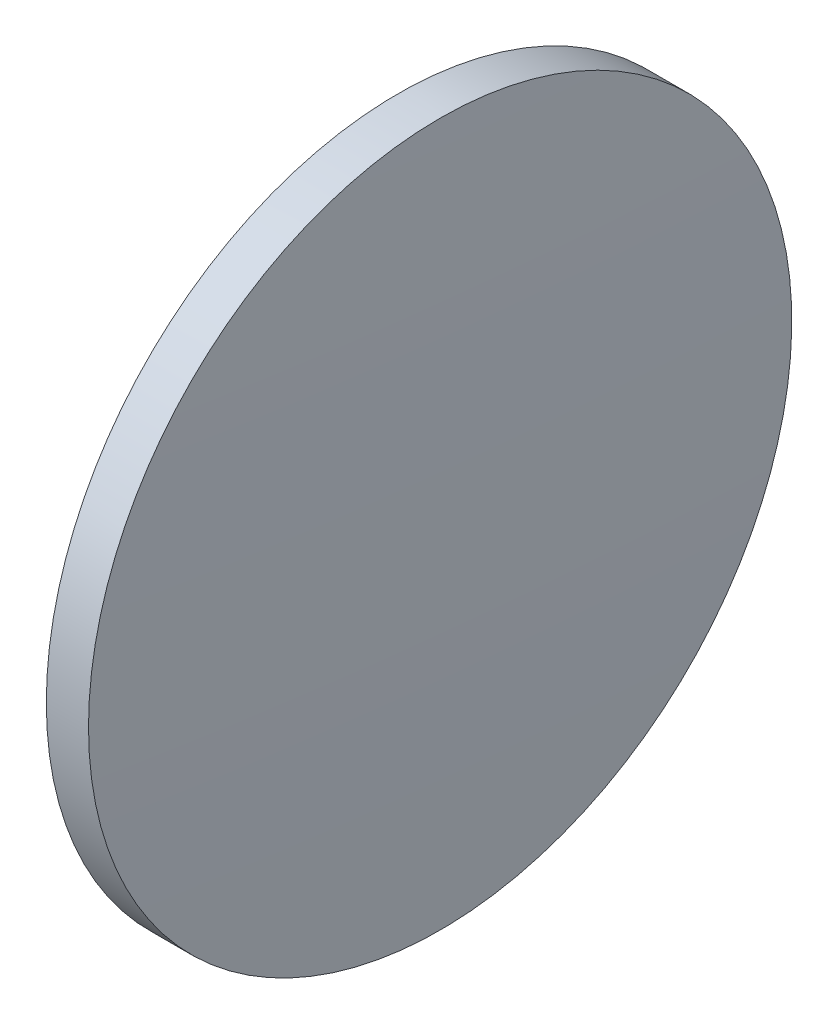
SolidWorks part; units mm, degrees
ref_plane "前视基准面" through (0, 0, 0) normal (0, 0, 1) x (1, 0, 0)
ref_plane "上视基准面" through (0, 0, 0) normal (0, 1, 0) x (1, 0, 0)
ref_plane "右视基准面" through (0, 0, 0) normal (1, 0, 0) x (0, 0, -1)
sketch "草图1" plane through (0, 0, 0) normal (0, 0, 1) x (1, 0, 0)
  line L0 (54.5309, 32.6296) -> (62.5594, 32.6296) construction
  line L1 (56.56, 32.6296) -> (56.56, 45.1296)
  line L2 (58.26, 32.6296) -> (56.56, 32.6296)
  line L5 (56.56, 45.1296) -> (58.06, 45.1296)
  arc A0 (58.26, 32.6296) -> (58.06, 45.1296) centre (-332.465, 32.6296) ccw
revolve "旋转1" add sketch "草图1" angle 360 about L0
